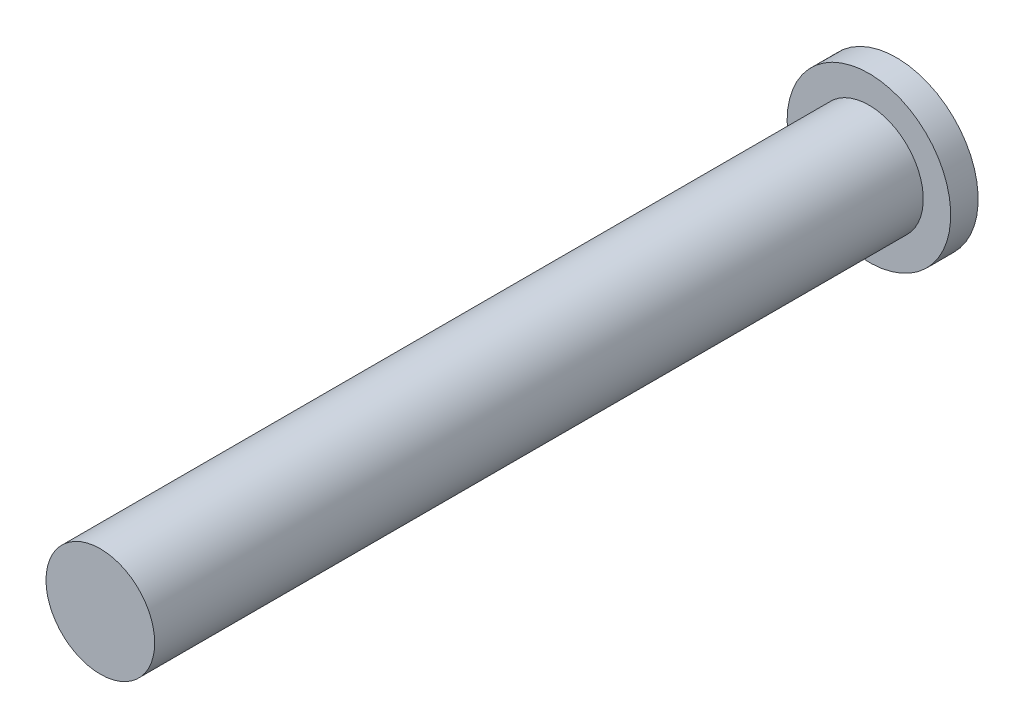
SolidWorks part; units mm, degrees
ref_plane "Front Plane" through (0, 0, 0) normal (0, 0, 1) x (1, 0, 0)
ref_plane "Top Plane" through (0, 0, 0) normal (0, 1, 0) x (1, 0, 0)
ref_plane "Right Plane" through (0, 0, 0) normal (1, 0, 0) x (0, 0, -1)
sketch "Sketch1" plane through (0, 0, 0) normal (0, 0, 1) x (1, 0, 0)
  circle A0 centre (0, 0) radius 4.95
  dimension "D1" = 9.9
extrude "Boss-Extrude1" add sketch "Sketch1" along normal blind 70
sketch "Sketch3" plane through (0, 0, 0) normal (0, 0, -1) x (-1, 0, 0)
  circle A2 centre (0, 0) radius 7.45
  circle A3 centre (0, 0) radius 7.45
  dimension "D1" = 2.5
extrude "Boss-Extrude2" add sketch "Sketch3" along normal blind 2.5
